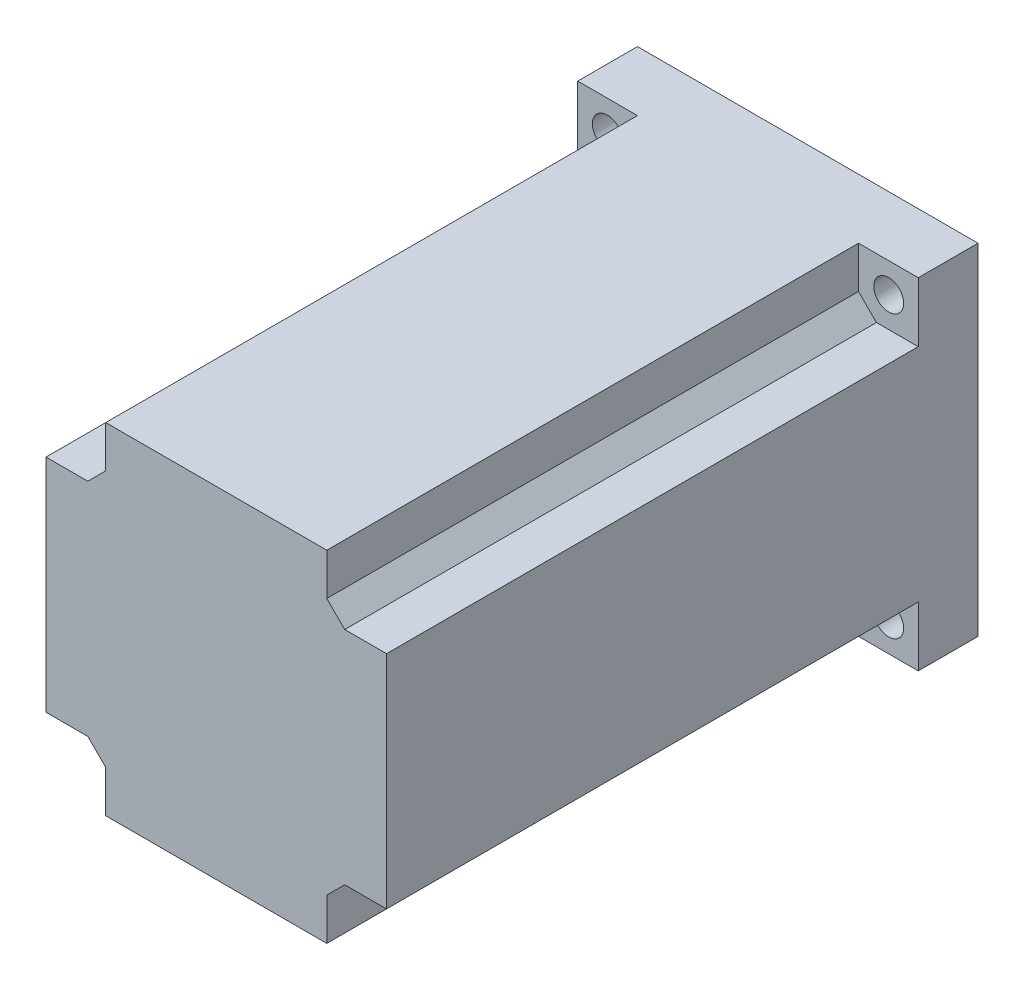
SolidWorks part; units mm, degrees
ref_plane "Front Plane" through (0, 0, 0) normal (0, 0, 1) x (1, 0, 0)
ref_plane "Top Plane" through (0, 0, 0) normal (0, 1, 0) x (1, 0, 0)
ref_plane "Right Plane" through (0, 0, 0) normal (1, 0, 0) x (0, 0, -1)
sketch "Sketch1" plane through (0, 0, 0) normal (0, 0, 1) x (1, 0, 0)
  line L0 (-28.5, 0) -> (28.5, 0) construction
  line L1 (-28.5, 28.5) -> (28.5, 28.5)
  line L2 (-28.5, 28.5) -> (-28.5, -28.5)
  line L3 (-28.5, -28.5) -> (28.5, -28.5)
  line L4 (28.5, 28.5) -> (28.5, -28.5)
  line L5 (-28.5, 28.5) -> (28.5, -28.5) construction
  line L6 (-28.5, -28.5) -> (28.5, 28.5) construction
  line L7 (0, 28.5) -> (0, -28.5) construction
  circle A0 centre (23.55, -23.55) radius 2.5
  circle A1 centre (23.55, 23.55) radius 2.5
  circle A2 centre (-23.55, 23.55) radius 2.5
  circle A3 centre (-23.55, -23.55) radius 2.5
  point P0 (0, 0)
  dimension "D3" = 5
  dimension "D4" = 23.55
  dimension "D1" = 57
  dimension "D2" = 57
extrude "Boss-Extrude2" add sketch "Sketch1" along normal blind 99
sketch "Sketch3" plane through (0, 0, 99) normal (0, 0, 1) x (1, 0, 0)
  line L0 (0, -28.5) -> (0, 28.5) construction
  line L1 (-28.5, 28.5) -> (-18.5, 28.5)
  line L2 (-28.5, 28.5) -> (-28.5, 18.5)
  line L3 (-28.5, 18.5) -> (-18.5, 18.5)
  line L4 (-18.5, 28.5) -> (-18.5, 18.5)
  line L17 (-28.5, 0) -> (28.5, 0) construction
  line L18 (-28.5, 28.5) -> (-28.5, -28.5) construction
  line L19 (28.5, -28.5) -> (28.5, 28.5) construction
  line L20 (-28.5, -28.5) -> (28.5, -28.5) construction
  line L21 (28.5, 28.5) -> (-28.5, 28.5) construction
  line L22 (-28.5, -18.5) -> (-18.5, -18.5)
  line L23 (-18.5, -28.5) -> (-18.5, -18.5)
  line L24 (-28.5, -28.5) -> (-18.5, -28.5)
  line L25 (-28.5, -28.5) -> (-28.5, -18.5)
  line L26 (28.5, -28.5) -> (28.5, -18.5)
  line L27 (28.5, -28.5) -> (18.5, -28.5)
  line L28 (18.5, -28.5) -> (18.5, -18.5)
  line L29 (28.5, -18.5) -> (18.5, -18.5)
  line L30 (28.5, 18.5) -> (18.5, 18.5)
  line L31 (18.5, 28.5) -> (18.5, 18.5)
  line L32 (28.5, 28.5) -> (18.5, 28.5)
  line L33 (28.5, 28.5) -> (28.5, 18.5)
  dimension "D1" = 10
  dimension "D2" = 10
extrude "Cut-Extrude1" cut sketch "Sketch3" against normal blind 89 contours L2 L1 L4 L3 | L30 L31 L32 L33 | L26 L29 L28 L27 | L22 L23 L24 L25
chamfer "Chamfer1" distance 3 angle 45 4 edges at (-18.5, 18.5, 54.5) (18.5, 18.5, 54.5) (18.5, -18.5, 54.5) (-18.5, -18.5, 54.5)
sketch "Sketch4" plane through (0, 0, 0) normal (0, 0, -1) x (-1, 0, 0)
  circle A0 centre (0, 0) radius 19.05
  dimension "D1" = 38.1
extrude "Boss-Extrude5" add sketch "Sketch4" along normal blind 1.6 contours A0
sketch "Sketch9" plane through (0, 0, -1.6) normal (0, 0, -1) x (-1, 0, 0)
  circle A0 centre (0, 0) radius 4.0256
  dimension "D1" = 8.0513
extrude "Cut-Extrude3" cut sketch "Sketch9" against normal blind 1.6
